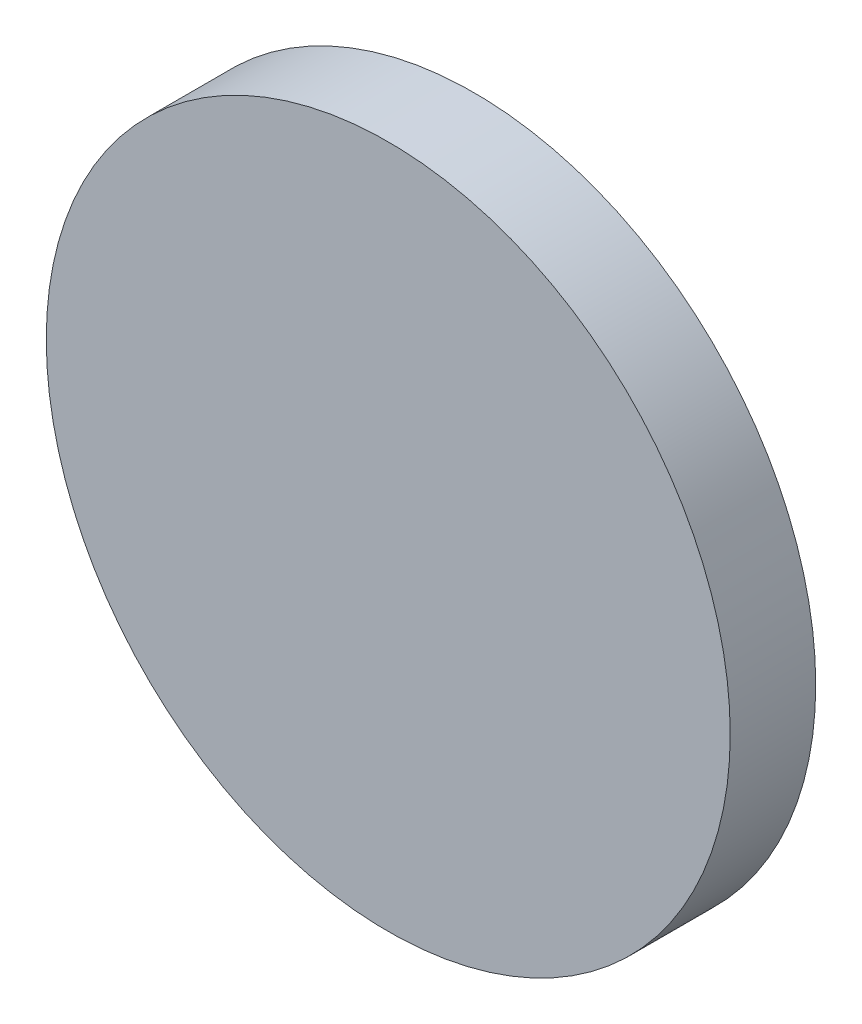
SolidWorks part; units mm, degrees
ref_plane "Front Plane" through (0, 0, 0) normal (0, 0, 1) x (1, 0, 0)
ref_plane "Top Plane" through (0, 0, 0) normal (0, 1, 0) x (1, 0, 0)
ref_plane "Right Plane" through (0, 0, 0) normal (1, 0, 0) x (0, 0, -1)
sketch "Sketch1" plane through (0, 0, 0) normal (0, 0, 1) x (1, 0, 0)
  circle A0 centre (0, 0) radius 3.175
  dimension "D1" = 6.35
extrude "Boss-Extrude1" add sketch "Sketch1" along normal blind 0.7937
